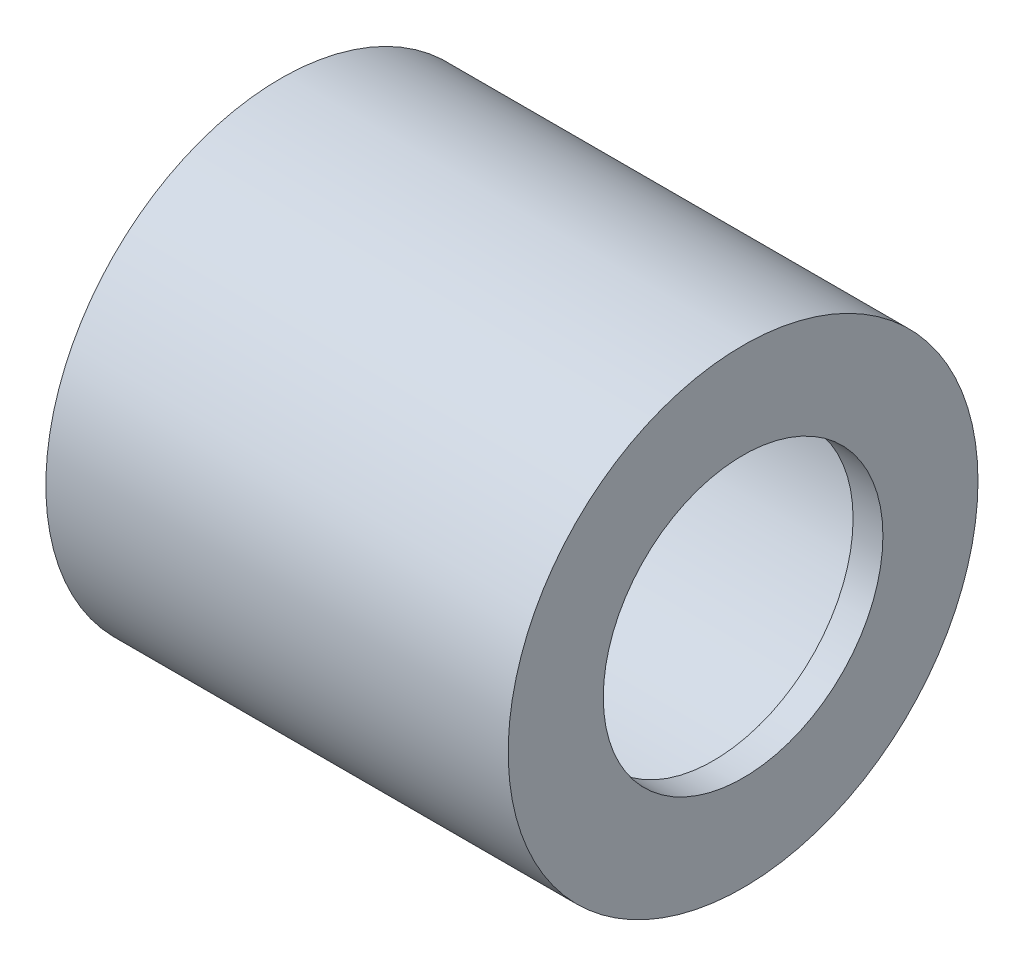
SolidWorks part; units mm, degrees
ref_plane "Front Plane" through (0, 0, 0) normal (0, 0, 1) x (1, 0, 0)
ref_plane "Top Plane" through (0, 0, 0) normal (0, 1, 0) x (1, 0, 0)
ref_plane "Right Plane" through (0, 0, 0) normal (1, 0, 0) x (0, 0, -1)
sketch "Sketch1" plane through (0, 0, 0) normal (1, 0, 0) x (0, 0, -1)
  circle A0 centre (0, 0) radius 4.0005
  dimension "D2" = 8.001
extrude "Extrude1" add sketch "Sketch1" along normal blind 7.874
sketch "Sketch2" plane through (0, 0, 0) normal (-1, 0, 0) x (0, 0, 1)
  circle A0 centre (0, 0) radius 3.6036
  circle A1 centre (0, 0) radius 4.0005 construction
  circle A2 centre (0, 0) radius 4.0005 construction
  dimension "D1" = 0.3969
extrude "Cut-Extrude1" cut sketch "Sketch2" against normal blind 7.366
sketch "Sketch3" plane through (7.366, 0, 0) normal (-1, 0, 0) x (0, 0, 1)
  circle A0 centre (0, 0) radius 2.3813
  dimension "D1" = 4.7625
extrude "Cut-Extrude2" cut sketch "Sketch3" against normal through all
